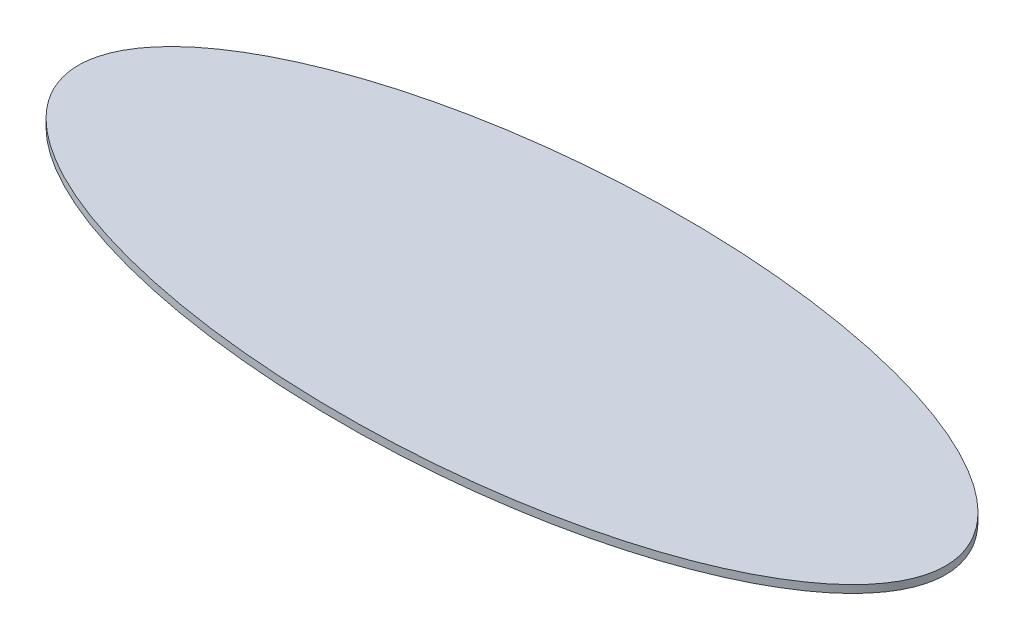
SolidWorks part; units mm, degrees
ref_plane "Front Plane" through (0, 0, 0) normal (0, 0, 1) x (1, 0, 0)
ref_plane "Top Plane" through (0, 0, 0) normal (0, 1, 0) x (1, 0, 0)
ref_plane "Right Plane" through (0, 0, 0) normal (1, 0, 0) x (0, 0, -1)
sketch "Sketch1" plane through (0, 0, 0) normal (0, 1, 0) x (1, 0, 0)
  ellipse E0 centre (0, 0) end of major axis (28.215, 0) minor radius 11.11
extrude "Boss-Extrude1" add sketch "Sketch1" along normal blind 0.5
